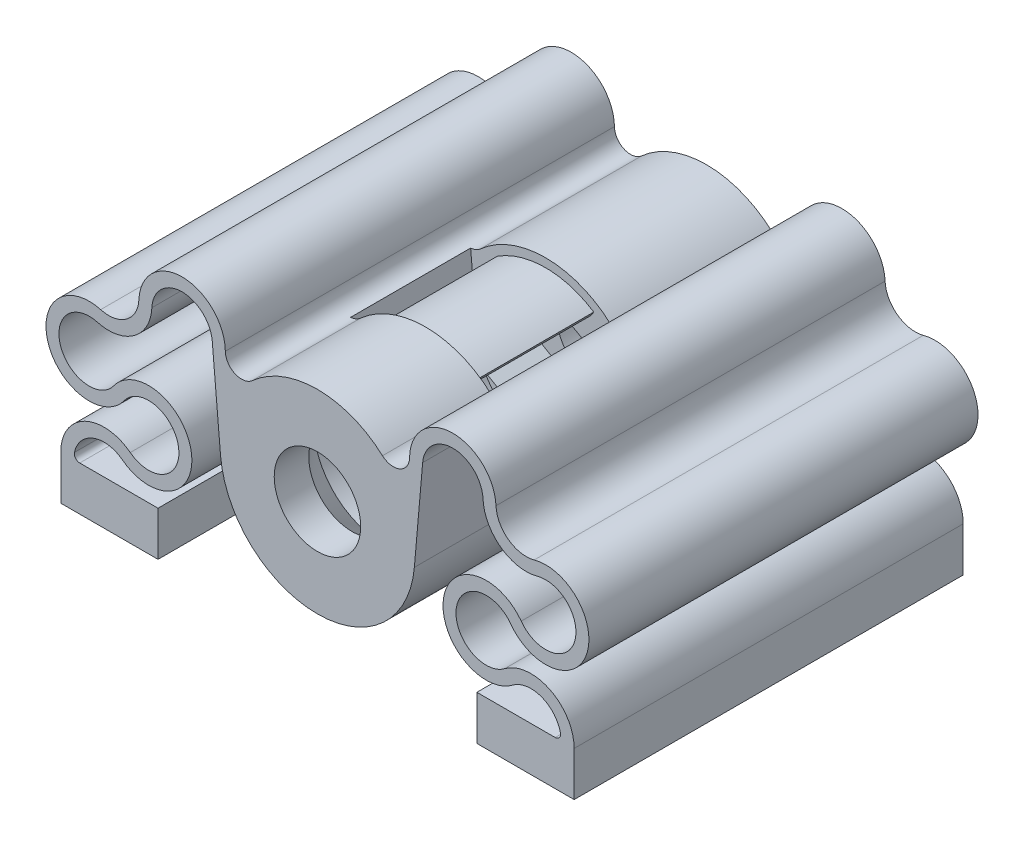
SolidWorks part; units mm, degrees
ref_plane "Front Plane" through (0, 0, 0) normal (0, 0, 1) x (1, 0, 0)
ref_plane "Top Plane" through (0, 0, 0) normal (0, 1, 0) x (1, 0, 0)
ref_plane "Right Plane" through (0, 0, 0) normal (1, 0, 0) x (0, 0, -1)
sketch "Sketch1" plane through (0, 0, 0) normal (0, 0, 1) x (1, 0, 0)
  line L0 (-14.75, -7.9) -> (-14.75, -12)
  line L1 (-21.995, -7.9) -> (-14.75, -7.9)
  line L2 (-23.75, -7.9) -> (-23.75, -12)
  line L3 (-23.75, -12) -> (-14.75, -12)
  line L4 (23.75, -7.9) -> (23.75, -12)
  line L5 (14.75, -7.9) -> (14.75, -12)
  line L6 (14.75, -12) -> (23.75, -12)
  line L7 (14.75, -7.9) -> (21.995, -7.9)
  line L8 (-14.75, -12) -> (14.75, -12) construction
  line L9 (0, -12) -> (0, 0) construction
  line L10 (-9.1862, 0) -> (0, 0) construction
  line L11 (2.8868, -5) -> (5.7735, 0) construction
  line L12 (5.7735, 0) -> (2.8868, 5) construction
  line L13 (2.8868, 5) -> (-2.8868, 5) construction
  line L14 (-2.8868, 5) -> (-5.7735, 0) construction
  line L15 (-5.7735, 0) -> (-2.8868, -5) construction
  line L16 (-2.8868, -5) -> (2.8868, -5) construction
  line L17 (-9.7338, 7.994) -> (-8.9658, -0.7844)
  line L18 (9.7338, 7.994) -> (8.9658, -0.7844)
  circle A0 centre (0, 0) radius 4
  arc A1 (-8.9658, -0.7844) -> (8.9658, -0.7844) centre (0, 0) ccw
  circle A2 centre (0, 0) radius 5 construction
  circle A3 centre (0, 0) radius 5.334 construction
  arc A4 (-20.3751, 4.2001) -> (-18.852, -0.1471) centre (-21.1163, 1.5) ccw
  arc A5 (-20.0574, 5.3573) -> (-17.8815, -0.8529) centre (-21.1163, 1.5) ccw
  arc A6 (-17.3189, -4.7235) -> (-17.8815, -0.8529) centre (-15.6172, -2.5) ccw
  arc A7 (-18.0483, -5.6765) -> (-18.852, -0.1471) centre (-15.6172, -2.5) ccw
  arc A8 (-17.3189, -4.7235) -> (-23.75, -7.9) centre (-19.75, -7.9) ccw
  arc A9 (-18.0483, -5.6765) -> (-22.483, -7.2913) centre (-19.75, -7.9) ccw
  arc A10 (-20.0574, 5.3573) -> (-16.519, 7.9308) centre (-19.3162, 8.0574) ccw
  arc A11 (-20.3751, 4.2001) -> (-15.3202, 7.8766) centre (-19.3162, 8.0574) ccw
  arc A12 (-6.02, 6.6902) -> (-8.5233, 7.7902) centre (-7.0234, 7.8053) cw
  arc A13 (18.0483, -5.6765) -> (22.483, -7.2913) centre (19.75, -7.9) cw
  arc A14 (17.3189, -4.7235) -> (23.75, -7.9) centre (19.75, -7.9) cw
  arc A15 (17.3189, -4.7235) -> (17.8815, -0.8529) centre (15.6172, -2.5) cw
  arc A16 (18.0483, -5.6765) -> (18.852, -0.1471) centre (15.6172, -2.5) cw
  arc A17 (9.7338, 7.994) -> (15.3202, 7.8766) centre (12.5231, 7.75) cw
  arc A18 (20.3751, 4.2001) -> (15.3202, 7.8766) centre (19.3162, 8.0574) cw
  arc A19 (20.3751, 4.2001) -> (18.852, -0.1471) centre (21.1163, 1.5) cw
  arc A20 (20.0574, 5.3573) -> (17.8815, -0.8529) centre (21.1163, 1.5) cw
  arc A21 (20.0574, 5.3573) -> (16.519, 7.9308) centre (19.3162, 8.0574) cw
  arc A22 (6.02, 6.6902) -> (-6.02, 6.6902) centre (0, 0) ccw
  arc A23 (22.483, -7.2913) -> (21.995, -7.9) centre (21.995, -7.4) cw
  arc A24 (-22.483, -7.2913) -> (-21.995, -7.9) centre (-21.995, -7.4) ccw
  arc A25 (-8.5233, 7.7902) -> (-16.519, 7.9308) centre (-12.5231, 7.75) ccw
  arc A26 (-9.7338, 7.994) -> (-15.3202, 7.8766) centre (-12.5231, 7.75) ccw
  arc A27 (8.5233, 7.7902) -> (16.519, 7.9308) centre (12.5231, 7.75) cw
  arc A28 (6.02, 6.6902) -> (8.5233, 7.7902) centre (7.0234, 7.8053) ccw
  point P55 (22.55, -7.9)
  point P58 (-22.55, -7.9)
  dimension "D5" = 8
  dimension "D6" = 18
  dimension "D7" = 10
  dimension "D8" = 5
  dimension "D9" = 1.2
  dimension "D10" = 8
  dimension "D11" = 1.5
  dimension "D15" = 0.5
  dimension "D14" = 19.75
  dimension "D1" = 12
  dimension "D2" = 47.5
  dimension "D3" = 9
  dimension "D4" = 4.1
  dimension "D12" = 9.5
  dimension "D13" = 13.5
extrude "Boss-Extrude1" add sketch "Sketch1" along normal blind 36
sketch "Sketch2" plane through (0, -12, 0) normal (0, -1, 0) x (1, 0, 0)
  line L0 (-19.225, 30.5) -> (19.225, 5.5) construction
  line L1 (0, 18) -> (23.75, 18) construction
  line L2 (23.75, 36) -> (23.75, 0) construction
  circle A0 centre (-19.225, 30.5) radius 2.6
  circle A1 centre (-19.225, 5.5) radius 2.6
  circle A2 centre (19.225, 5.5) radius 2.6
  circle A3 centre (19.225, 30.5) radius 2.6
  dimension "D3" = 5.2
  dimension "D1" = 38.45
  dimension "D2" = 25
extrude "Cut-Extrude1" cut sketch "Sketch2" against normal blind 4.2
sketch "Sketch3" plane through (0, 0, 36) normal (0, 0, 1) x (1, 0, 0)
  line L0 (-7.009, 7.2547) -> (-6.3258, -0.5534)
  line L2 (0, 0) -> (0, 11.2231) construction
  line L3 (6.3258, -0.5534) -> (7.009, 7.2547)
  line L4 (-9.7338, 7.994) -> (-8.9658, -0.7844) construction
  line L5 (8.9658, -0.7844) -> (9.7338, 7.994) construction
  arc A0 (-6.3258, -0.5534) -> (6.3258, -0.5534) centre (0, 0) ccw
  arc A1 (7.009, 7.2547) -> (-7.009, 7.2547) centre (0, 0) ccw
  dimension "D1" = 12.7
extrude "Cut-Extrude2" cut sketch "Sketch3" against normal blind 11.1 from offset 10 offset against normal yes
sketch "Sketch4" plane through (0, 0, 0) normal (0, 1, 0) x (1, 0, 0)
  line L0 (0, -14.9) -> (0, -36.0496) construction
  line L1 (-4, -14.9) -> (4, -14.9) construction
  line L2 (0, -14.9) -> (-6.35, -14.9)
  line L4 (-6.35, -14.9) -> (-6.35, -30)
  line L5 (-6.35, -30) -> (-1.2738, -36.0496)
  line L6 (-1.2738, -36.0496) -> (0, -36.0496)
  line L7 (0, -36.0496) -> (0, -14.9)
  line L9 (6.3258, -26) -> (-6.3258, -26) construction
  line L10 (-6.3258, -14.9) -> (6.3258, -14.9) construction
  dimension "D1" = 6.35
  dimension "D2" = 40
  dimension "D3" = 4
revolve "Cut-Revolve1" cut sketch "Sketch4" angle 360 about L0
sketch "Sketch5" plane through (0, 0, 14.9) normal (0, 0, 1) x (1, 0, 0)
  line L1 (5.35, -3.0888) -> (5.35, 3.0888)
  line L2 (5.35, 3.0888) -> (0, 6.1776)
  line L3 (0, 6.1776) -> (-5.35, 3.0888)
  line L4 (-5.35, 3.0888) -> (-5.35, -3.0888)
  line L5 (-5.35, -3.0888) -> (0, -6.1776)
  line L6 (0, -6.1776) -> (5.35, -3.0888)
  circle A0 centre (0, 0) radius 5.35 construction
  dimension "D1" = 10.7
extrude "Cut-Extrude3" cut sketch "Sketch5" against normal blind 5
sketch "Sketch6" plane through (0, 0, 14.9) normal (0, 0, 1) x (1, 0, 0)
  line L0 (-4.466, 6.8771) -> (-4.1937, 6.4578)
  line L1 (4.1937, 6.4578) -> (4.466, 6.8771)
  line L5 (6.3258, -0.5534) -> (6.9262, 6.3084) construction
  line L6 (-6.9262, 6.3084) -> (-6.3258, -0.5534) construction
  arc A0 (4.1937, 6.4578) -> (-4.1937, 6.4578) centre (0, 0) ccw
  arc A1 (4.466, 6.8771) -> (-4.466, 6.8771) centre (0, 0) ccw
  dimension "D3" = 8.2
  dimension "D1" = 28
  dimension "D2" = 0.5
  dimension "D4" = 28
extrude "Boss-Extrude2" add sketch "Sketch6" along normal up to surface (11.1 mm away) up to face at (0, 5.6585, 26)
